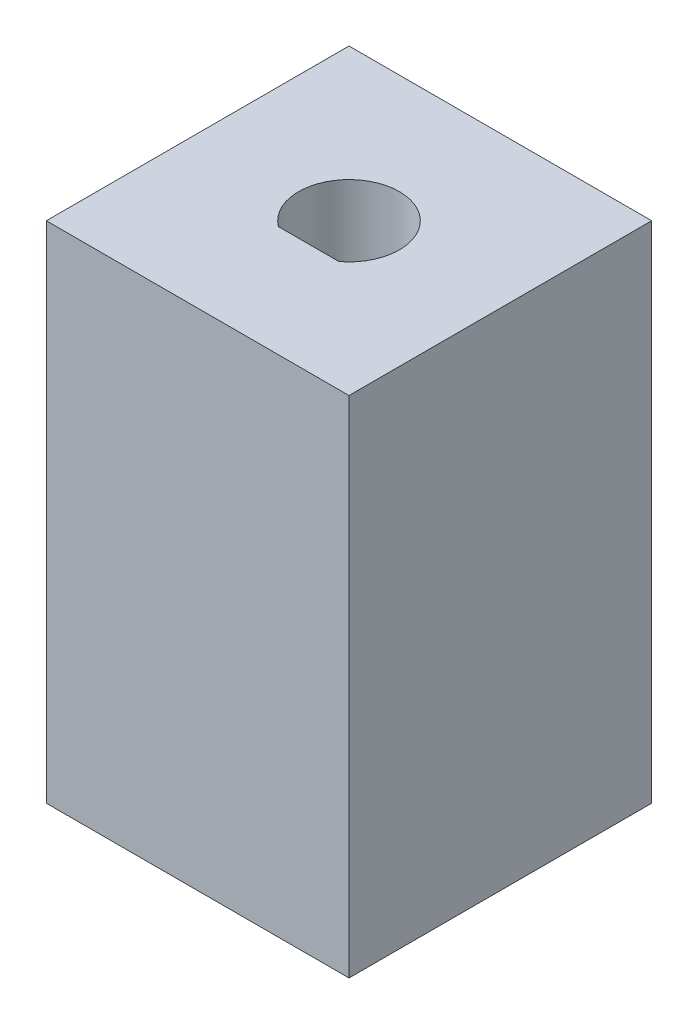
SolidWorks part; units mm, degrees
ref_plane "Front Plane" through (0, 0, 0) normal (0, 0, 1) x (1, 0, 0)
ref_plane "Top Plane" through (0, 0, 0) normal (0, 1, 0) x (1, 0, 0)
ref_plane "Right Plane" through (0, 0, 0) normal (1, 0, 0) x (0, 0, -1)
sketch "Sketch1" plane through (0, 0, 0) normal (0, 1, 0) x (1, 0, 0)
  line L1 (0, 0) -> (15, 0)
  line L2 (0, 0) -> (0, 15)
  line L3 (0, 15) -> (15, 15)
  line L4 (15, 0) -> (15, 15)
  dimension "D1" = 15
  dimension "D2" = 15
extrude "Boss-Extrude1" add sketch "Sketch1" along normal blind 25
sketch "Sketch2" plane through (0, 25, 0) normal (0, 1, 0) x (1, 0, 0)
  line L0 (0, 0) -> (15, 0) construction
  line L1 (0, 15) -> (0, 0) construction
  line L2 (6, 5.5) -> (9, 5.5)
  arc A0 (9, 5.5) -> (6, 5.5) centre (7.5, 7.5) ccw
  point P4 (7.5, 0)
  point P7 (0, 7.5)
  dimension "D1" = 5
  dimension "D2" = 2
extrude "Cut-Extrude1" cut sketch "Sketch2" against normal blind 20
